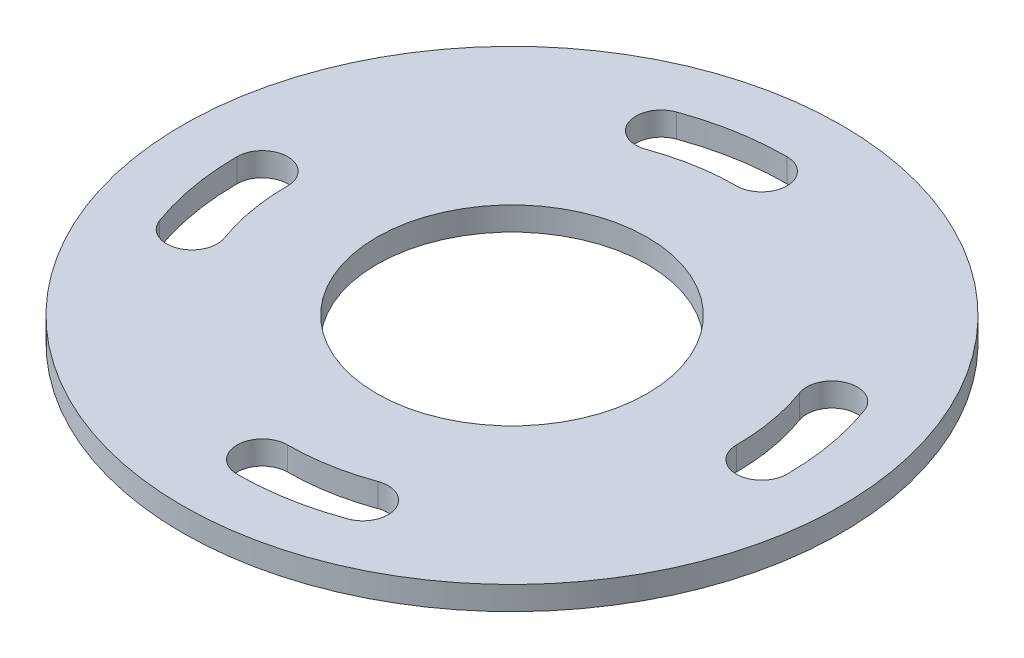
SolidWorks part; units mm, degrees
ref_plane "Front Plane" through (0, 0, 0) normal (0, 0, 1) x (1, 0, 0)
ref_plane "Top Plane" through (0, 0, 0) normal (0, 1, 0) x (1, 0, 0)
ref_plane "Right Plane" through (0, 0, 0) normal (1, 0, 0) x (0, 0, -1)
sketch "Sketch1" plane through (0, 0, 0) normal (0, 1, 0) x (1, 0, 0)
  circle A0 centre (0, 0) radius 11.5
  circle A1 centre (0, 0) radius 28
  dimension "D1" = 23
  dimension "D2" = 56
extrude "Boss-Extrude1" add sketch "Sketch1" along normal blind 2
sketch "Sketch2" plane through (0, 2, 0) normal (0, 1, 0) x (1, 0, 0)
  line L0 (0, 0) -> (36.5985, 0) construction
  line L1 (0, 0) -> (38.0098, 13.8344) construction
  line L3 (-15, -15) -> (15, -15) construction
  line L4 (-15, -15) -> (-15, 15) construction
  line L5 (-15, 15) -> (15, 15) construction
  line L6 (15, -15) -> (15, 15) construction
  line L7 (-15, -15) -> (15, 15) construction
  line L8 (-15, 15) -> (15, -15) construction
  circle A0 centre (0, 0) radius 21.2132 construction
  arc A1 (21.9542, 7.9907) -> (17.9136, 6.52) centre (19.9339, 7.2553) ccw
  arc A2 (19.0632, 0) -> (23.3632, 0) centre (21.2132, 0) ccw
  arc A3 (23.3632, 0) -> (21.9542, 7.9907) centre (0, 0) ccw
  arc A4 (19.0632, 0) -> (17.9136, 6.52) centre (0, 0) ccw
  point P10 (-41.0257, 20.8761)
  dimension "D3" = 4.3
  dimension "D1" = 30
  dimension "D2" = 20
extrude "Cut-Extrude1" cut sketch "Sketch2" against normal through all
pattern_circular "CirPattern1" count 4 every 90 about axis through (0, 0, 0) along (0, 1, 0) of "Cut-Extrude1"
